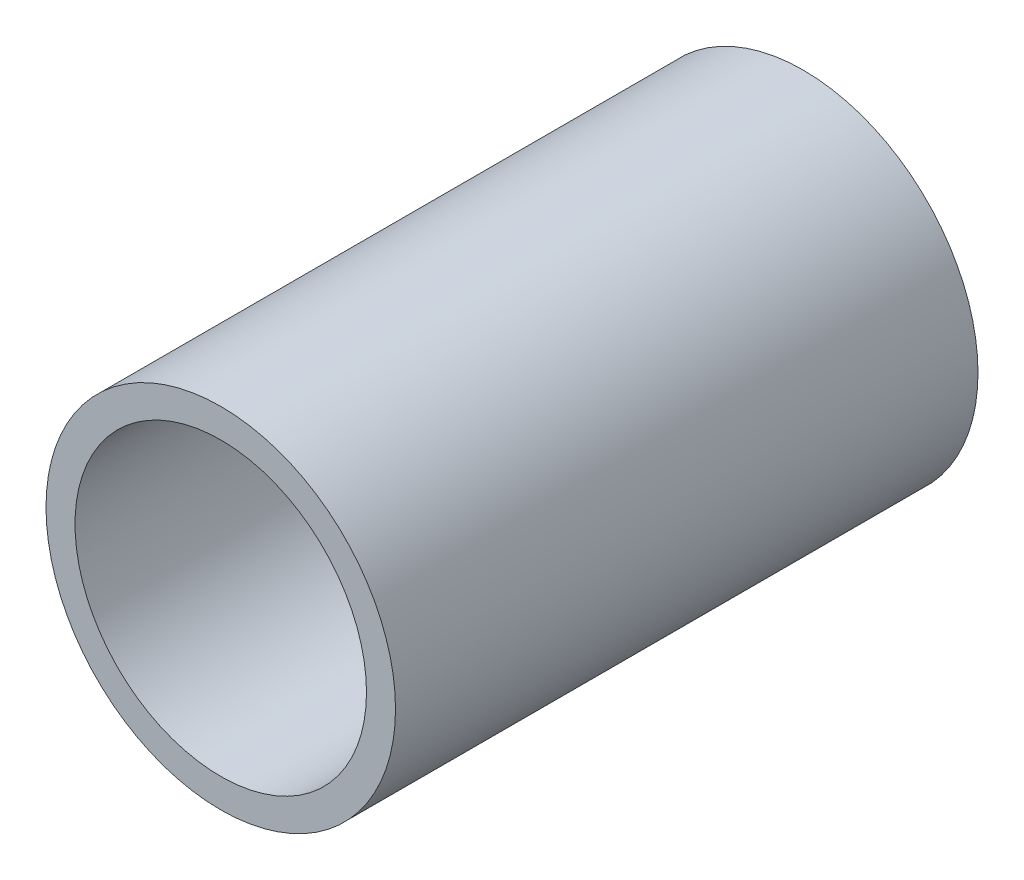
SolidWorks part; units mm, degrees
material "Nylon 101"
ref_plane "Front Plane" through (0, 0, 0) normal (0, 0, 1) x (1, 0, 0)
ref_plane "Top Plane" through (0, 0, 0) normal (0, 1, 0) x (1, 0, 0)
ref_plane "Right Plane" through (0, 0, 0) normal (1, 0, 0) x (0, 0, -1)
sketch "Sketch1" plane through (0, 0, 0) normal (0, 0, 1) x (1, 0, 0)
  circle A0 centre (0, 0) radius 19.05
  circle A1 centre (0, 0) radius 15.8877
  dimension "D1" = 38.1
  dimension "ID" = 31.7754
extrude "Extrude1" add sketch "Sketch1" along normal mid plane 63.5
sketch "Sketch2" plane through (0, 0, 0) normal (1, 0, 0) x (0, 0, -1)
  line L0 (-31.75, -15.8877) -> (31.75, -15.8877) construction
  line L3 (31.75, 15.8877) -> (-31.75, 15.8877) construction
  line L5 (-31.75, -15.8877) -> (31.75, -15.8877)
  line L6 (31.75, 15.8877) -> (-31.75, 15.8877)
sketch "Sketch4" plane through (0, 0, 31.75) normal (0, 0, 1) x (1, 0, 0)
  line L0 (0, 0) -> (-11.2343, 11.2343)
  line L1 (0, -55) -> (0, 55) construction
  circle A0 centre (0, 0) radius 15.8877 construction
  dimension "D1" = 45
